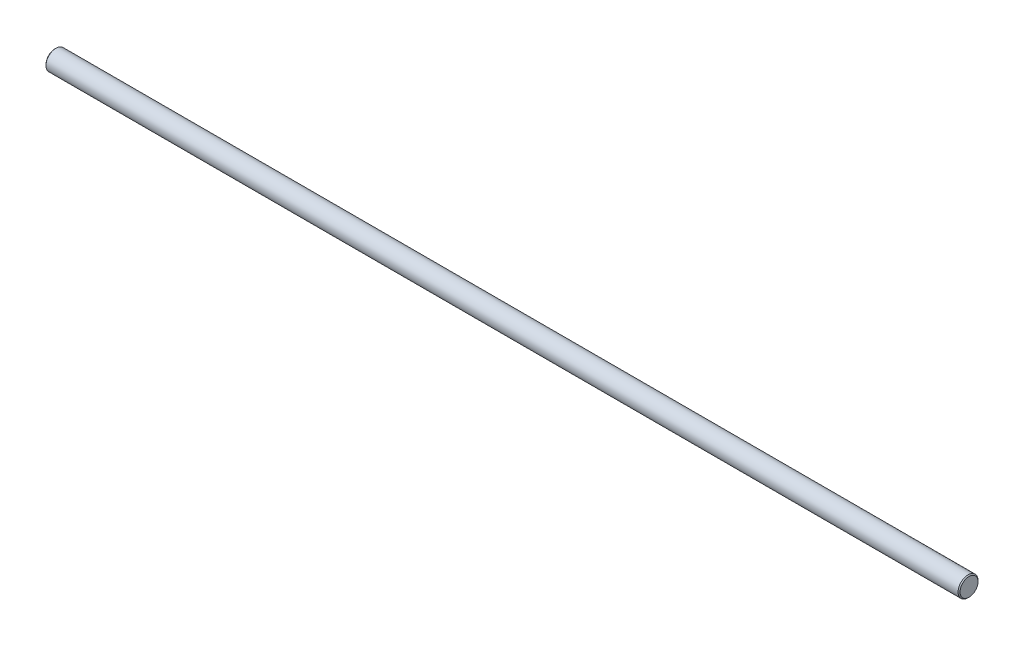
SolidWorks part; units mm, degrees
ref_plane "Front Plane" through (0, 0, 0) normal (0, 0, 1) x (1, 0, 0)
ref_plane "Top Plane" through (0, 0, 0) normal (0, 1, 0) x (1, 0, 0)
ref_plane "Right Plane" through (0, 0, 0) normal (1, 0, 0) x (0, 0, -1)
ref_plane "Plane1" through (0, 0, 0) normal (0, 0, 1) x (1, 0, 0)
sketch "Sketch1" plane through (0, 0, 0) normal (0, 0, 1) x (1, 0, 0)
  line L0 (0, 0) -> (0, 4.5)
  line L1 (0, 4.5) -> (0.5, 5)
  line L2 (0.5, 5) -> (457.5, 5)
  line L3 (457.5, 5) -> (458, 4.5)
  line L4 (458, 4.5) -> (458, 0)
  line L5 (458, 0) -> (0, 0)
  line L6 (458, 0) -> (0, 0) construction
revolve "Revolve1" add sketch "Sketch1" angle 360 about L6
ref_plane "Plane2" through (229, 0, 0) normal (-1, 0, 0) x (0, 0, 1)
